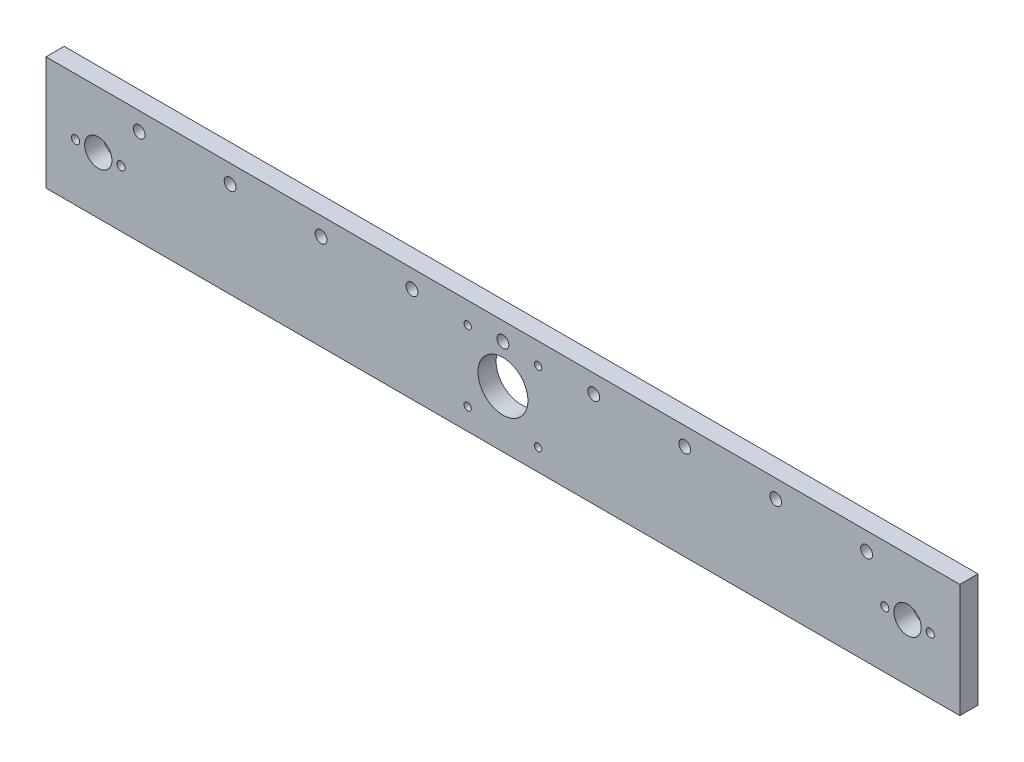
SolidWorks part; units mm, degrees
ref_plane "Front Plane" through (0, 0, 0) normal (0, 0, 1) x (1, 0, 0)
ref_plane "Top Plane" through (0, 0, 0) normal (0, 1, 0) x (1, 0, 0)
ref_plane "Right Plane" through (0, 0, 0) normal (1, 0, 0) x (0, 0, -1)
sketch "Sketch1" plane through (0, 0, 0) normal (0, 0, 1) x (1, 0, 0)
  line L0 (0, 0) -> (-200, 0) construction
  line L1 (-201, -25) -> (201, -25)
  line L2 (-201, -25) -> (-201, 25)
  line L3 (-201, 25) -> (201, 25)
  line L4 (201, -25) -> (201, 25)
  line L5 (-201, -25) -> (201, 25) construction
  line L6 (-201, 25) -> (201, -25) construction
  line L7 (0, 24) -> (0, -26) construction
  line L8 (-15.5, -15.5) -> (15.5, -15.5) construction
  line L9 (-15.5, -15.5) -> (-15.5, 15.5) construction
  line L10 (-15.5, 15.5) -> (15.5, 15.5) construction
  line L11 (15.5, -15.5) -> (15.5, 15.5) construction
  line L12 (-15.5, -15.5) -> (15.5, 15.5) construction
  line L13 (-15.5, 15.5) -> (15.5, -15.5) construction
  circle A0 centre (-178, 0) radius 6
  circle A1 centre (168, 0) radius 1.8
  circle A2 centre (0, 0) radius 11
  circle A3 centre (-188, 0) radius 1.8
  circle A4 centre (-168, 0) radius 1.8
  circle A5 centre (188, 0) radius 1.8
  circle A6 centre (178, 0) radius 6
  circle A7 centre (-15.5, 15.5) radius 1.6
  circle A8 centre (15.5, 15.5) radius 1.6
  circle A9 centre (-15.5, -15.5) radius 1.6
  circle A10 centre (15.5, -15.5) radius 1.6
  circle A11 centre (0, 17) radius 2.6
  circle A12 centre (40, 17) radius 2.6
  circle A13 centre (80, 17) radius 2.6
  circle A14 centre (120, 17) radius 2.6
  circle A15 centre (160, 17) radius 2.6
  circle A16 centre (-40, 17) radius 2.6
  circle A17 centre (-80, 17) radius 2.6
  circle A18 centre (-120, 17) radius 2.6
  circle A19 centre (-160, 17) radius 2.6
  point P0 (0, 0)
  dimension "D1" = 50
  dimension "D2" = 402
  dimension "D3" = 178
  dimension "D4" = 10
  dimension "D5" = 10
  dimension "D6" = 31
  dimension "D7" = 31
  dimension "D8" = 8
  dimension "D9" = 178
extrude "Boss-Extrude1" add sketch "Sketch1" along normal blind 8 contours L3 L4 L1 L2
